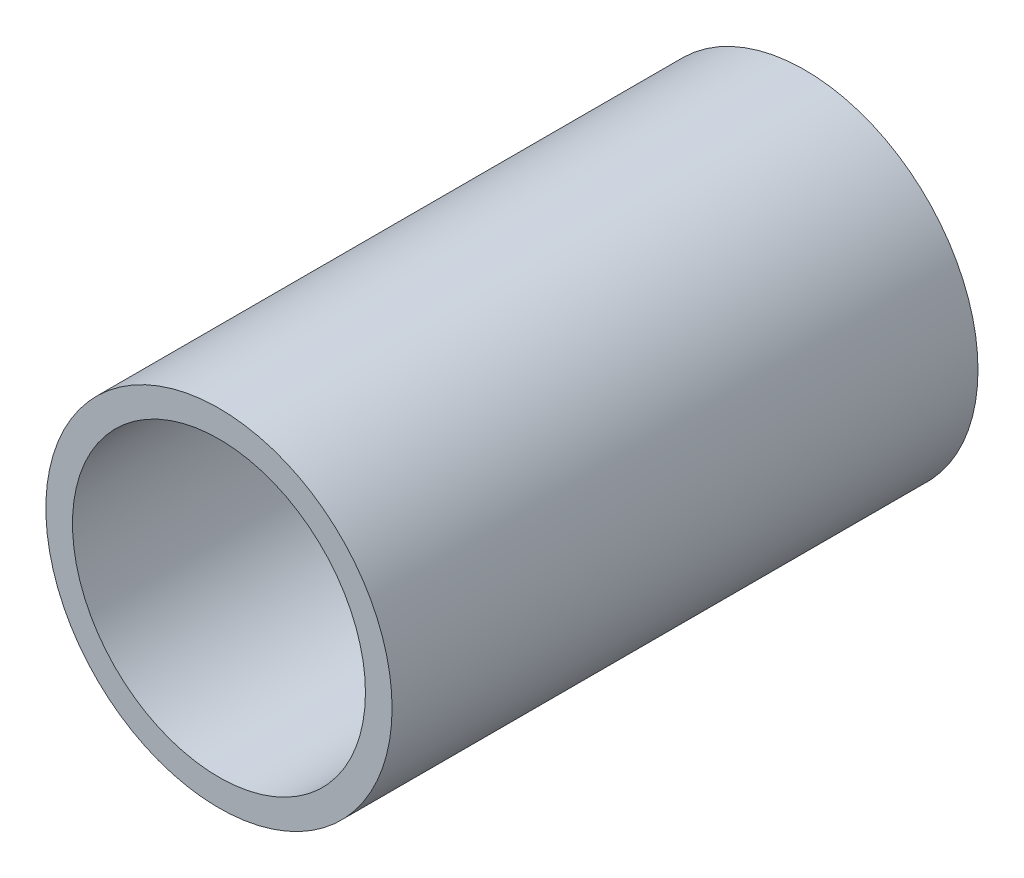
SolidWorks part; units mm, degrees
material "Rubber"
ref_plane "Front Plane" through (0, 0, 0) normal (0, 0, 1) x (1, 0, 0)
ref_plane "Top Plane" through (0, 0, 0) normal (0, 1, 0) x (1, 0, 0)
ref_plane "Right Plane" through (0, 0, 0) normal (1, 0, 0) x (0, 0, -1)
sketch "Sketch1" plane through (0, 0, 0) normal (0, 0, 1) x (1, 0, 0)
  circle A0 centre (0, 0) radius 3.25
  circle A1 centre (0, 0) radius 2.75
  dimension "D1" = 6.5
  dimension "D2" = 5.5
extrude "Boss-Extrude1" add sketch "Sketch1" along normal blind 11
